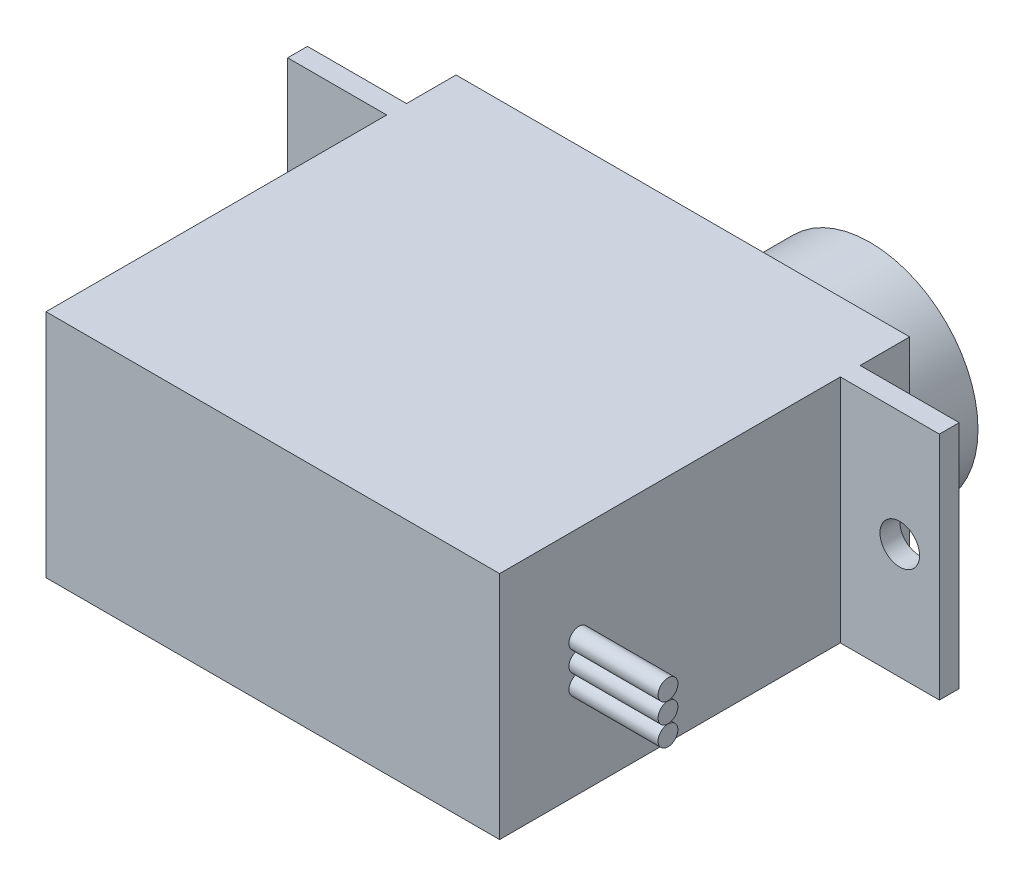
SolidWorks part; units mm, degrees
ref_plane "Front Plane" through (0, 0, 0) normal (0, 0, 1) x (1, 0, 0)
ref_plane "Top Plane" through (0, 0, 0) normal (0, 1, 0) x (1, 0, 0)
ref_plane "Right Plane" through (0, 0, 0) normal (1, 0, 0) x (0, 0, -1)
sketch "Sketch1" plane through (0, 0, 0) normal (0, 1, 0) x (1, 0, 0)
  line L1 (0, 0) -> (22.9, 0)
  line L2 (0, 0) -> (0, 20.7)
  line L3 (0, 20.7) -> (22.9, 20.7)
  line L4 (22.9, 0) -> (22.9, 20.7)
  dimension "D1" = 22.9
  dimension "D2" = 20.7
extrude "Boss-Extrude1" add sketch "Sketch1" along normal blind 11.63
sketch "Sketch3" plane through (0, 0, -20.7) normal (0, 0, -1) x (-1, 0, 0)
  line L0 (-22.9, 11.63) -> (-22.9, 0) construction
  line L1 (-22.9, 0) -> (0, 0) construction
  line L2 (-22.9, 0) -> (-22.9, 11.63) construction
  circle A0 centre (-17.4, 5.815) radius 5.45
  point P2 (-22.9, 5.815)
  dimension "D2" = 10.9
  dimension "D1" = 5.5
  dimension "D3" = 5.815
  dimension "D4" = 11.63
extrude "Boss-Extrude2" add sketch "Sketch3" along normal blind 3.5
ref_plane "Plane1" through (11.45, 0, 0) normal (-1, 0, 0) x (0, 0, 1)
sketch "Sketch4" plane through (22.9, 0, 0) normal (1, 0, 0) x (0, 0, -1)
  line L0 (0, 11.63) -> (20.7, 11.63) construction
  line L1 (18.2, 11.63) -> (17.2, 11.63)
  line L2 (18.2, 11.63) -> (18.2, 0)
  line L3 (18.2, 0) -> (17.2, 0)
  line L4 (17.2, 11.63) -> (17.2, 0)
  line L5 (0, 0) -> (20.7, 0) construction
  line L6 (20.7, 11.63) -> (20.7, 0) construction
  dimension "D1" = 3.5
  dimension "D2" = 1
extrude "Boss-Extrude3" add sketch "Sketch4" along normal blind 5
sketch "Sketch5" plane through (0, 0, -18.2) normal (0, 0, -1) x (-1, 0, 0)
  line L0 (-27.9, 5.815) -> (-22.9, 5.815) construction
  line L1 (-27.9, 0) -> (-27.9, 11.63) construction
  line L2 (-22.9, 0) -> (-22.9, 11.63) construction
  circle A0 centre (-25.9, 5.815) radius 1
  dimension "D1" = 2
  dimension "D2" = 2
extrude "Cut-Extrude1" cut sketch "Sketch5" against normal up to next (1 mm away)
mirror "Mirror1" about plane through (11.45, 0, 0) normal (-1, 0, 0) of "Cut-Extrude1", "Boss-Extrude3"
sketch "Sketch6" plane through (0, 0, -24.2) normal (0, 0, -1) x (-1, 0, 0)
  line L0 (-17.4, 5.815) -> (-17.4, 7.815) construction
  line L1 (-17.4, 5.815) -> (-17.0715, 7.4666) construction
  line L2 (-17.4, 5.815) -> (-17.7285, 7.4666) construction
  line L3 (-17.4, 7.815) -> (-17.7285, 7.4666)
  line L4 (-17.4, 7.815) -> (-17.0715, 7.4666)
  line L6 (-16.6346, 7.6628) -> (-16.4644, 7.2152)
  line L7 (-16.6346, 7.6628) -> (-17.0715, 7.4666)
  line L8 (-15.9858, 7.2292) -> (-15.9998, 6.7506)
  line L9 (-15.9858, 7.2292) -> (-16.4644, 7.2152)
  line L10 (-15.5522, 6.5804) -> (-15.7484, 6.1435)
  line L11 (-15.5522, 6.5804) -> (-15.9998, 6.7506)
  line L12 (-15.4, 5.815) -> (-15.7484, 5.4865)
  line L13 (-15.4, 5.815) -> (-15.7484, 6.1435)
  line L14 (-15.5522, 5.0496) -> (-15.9998, 4.8794)
  line L15 (-15.5522, 5.0496) -> (-15.7484, 5.4865)
  line L16 (-15.9858, 4.4008) -> (-16.4644, 4.4148)
  line L17 (-15.9858, 4.4008) -> (-15.9998, 4.8794)
  line L18 (-16.6346, 3.9672) -> (-17.0715, 4.1634)
  line L19 (-16.6346, 3.9672) -> (-16.4644, 4.4148)
  line L20 (-17.4, 3.815) -> (-17.7285, 4.1634)
  line L21 (-17.4, 3.815) -> (-17.0715, 4.1634)
  line L22 (-18.1654, 3.9672) -> (-18.3356, 4.4148)
  line L23 (-18.1654, 3.9672) -> (-17.7285, 4.1634)
  line L24 (-18.8142, 4.4008) -> (-18.8002, 4.8794)
  line L25 (-18.8142, 4.4008) -> (-18.3356, 4.4148)
  line L26 (-19.2478, 5.0496) -> (-19.0516, 5.4865)
  line L27 (-19.2478, 5.0496) -> (-18.8002, 4.8794)
  line L28 (-19.4, 5.815) -> (-19.0516, 6.1435)
  line L29 (-19.4, 5.815) -> (-19.0516, 5.4865)
  line L30 (-19.2478, 6.5804) -> (-18.8002, 6.7506)
  line L31 (-19.2478, 6.5804) -> (-19.0516, 6.1435)
  line L32 (-18.8142, 7.2292) -> (-18.3356, 7.2152)
  line L33 (-18.8142, 7.2292) -> (-18.8002, 6.7506)
  line L34 (-18.1654, 7.6628) -> (-17.7285, 7.4666)
  line L35 (-18.1654, 7.6628) -> (-18.3356, 7.2152)
  dimension "D1" = 2
  dimension "D2" = 22.5
  dimension "D3" = 11.25
  dimension "D4" = 16
extrude "Boss-Extrude4" add sketch "Sketch6" along normal blind 2.2
sketch "Sketch8" plane through (22.9, 0, 0) normal (1, 0, 0) x (0, 0, -1)
  line L0 (0, 5.815) -> (20.7, 5.815) construction
  line L1 (0, 11.63) -> (0, 0) construction
  line L2 (20.7, 11.63) -> (20.7, 0) construction
  circle A0 centre (4, 5.815) radius 0.5
  dimension "D1" = 1
  dimension "D2" = 4
extrude "Boss-Extrude6" add sketch "Sketch8" along normal blind 4.5
sketch "Sketch9" plane through (22.9, 0, 0) normal (1, 0, 0) x (0, 0, -1)
  line L0 (4, 5.815) -> (4, 7.5439) construction
  circle A0 centre (4, 6.825) radius 0.5
  dimension "D1" = 1
  dimension "D2" = 1.01
sketch "Sketch10" plane through (22.9, 0, 0) normal (1, 0, 0) x (0, 0, -1)
  line L0 (4, 5.815) -> (4, 4.0882) construction
  circle A0 centre (4, 4.805) radius 0.5
  dimension "D1" = 1
  dimension "D2" = 1.01
extrude "Boss-Extrude9" add sketch "Sketch10" along normal blind 4.5
extrude "Boss-Extrude10" add sketch "Sketch9" along normal blind 4.5
sketch "Sketch13" plane through (0, 0, -26.4) normal (0, 0, -1) x (-1, 0, 0)
  circle A0 centre (-17.4, 5.815) radius 0.5
  dimension "D1" = 1
extrude "Cut-Extrude2" cut sketch "Sketch13" against normal up to surface (2.2 mm away) up to face at (11.95, 5.815, -24.2)
equation "\"D3@Sketch3\" = \"D4@Sketch3\"/2"
